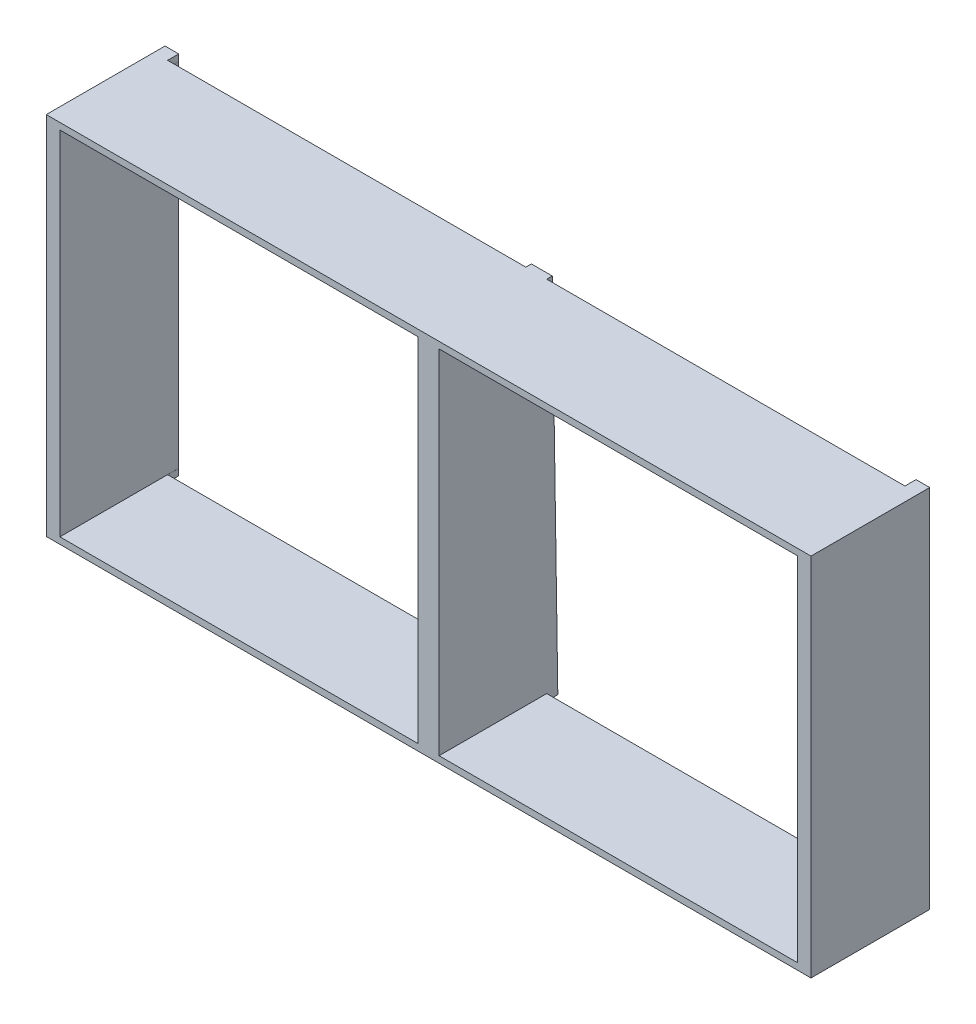
SolidWorks part; units mm, degrees
ref_plane "Спереди" through (0, 0, 0) normal (0, 0, 1) x (1, 0, 0)
ref_plane "Сверху" through (0, 0, 0) normal (0, 1, 0) x (1, 0, 0)
ref_plane "Справа" through (0, 0, 0) normal (1, 0, 0) x (0, 0, -1)
sketch "Эскиз1" plane through (0, 0, 0) normal (0, 0, 1) x (1, 0, 0)
  line L1 (-2930, 1400) -> (2930, 1400)
  line L2 (-2930, 1400) -> (-2930, -1400)
  line L3 (-2930, -1400) -> (2930, -1400)
  line L4 (2930, 1400) -> (2930, -1400)
  line L5 (-2930, 1400) -> (2930, -1400) construction
  line L6 (-2930, -1400) -> (2930, 1400) construction
  line L7 (-2825.3571, 1350) -> (-80, 1350)
  line L8 (-2825.3571, 1350) -> (-2825.3571, -1350)
  line L9 (-2825.3571, -1350) -> (-80, -1350)
  line L10 (-80, 1350) -> (-80, -1350)
  line L11 (80, 1350) -> (2825.3571, 1350)
  line L12 (80, 1350) -> (80, -1350)
  line L13 (80, -1350) -> (2825.3571, -1350)
  line L14 (2825.3571, 1350) -> (2825.3571, -1350)
  point P0 (0, 0)
extrude "Бобышка-Вытянуть1" add sketch "Эскиз1" along normal blind 910
sketch "Эскиз2" plane through (0, -1400, 0) normal (0, -1, 0) x (1, 0, 0)
  line L2 (-2825, 85) -> (-80, 85)
  line L3 (-2825, 85) -> (-2825, 0)
  line L4 (-2825, 0) -> (-80, 0)
  line L5 (-80, 85) -> (-80, 0)
  line L6 (-2825, 85) -> (-80, 0) construction
  line L7 (-2825, 0) -> (-80, 85) construction
  line L8 (0, 424.0898) -> (0, -233.7336) construction
  line L9 (2825, 0) -> (80, 85) construction
  line L10 (2825, 85) -> (80, 0) construction
  line L11 (80, 85) -> (80, 0)
  line L12 (2825, 0) -> (80, 0)
  line L13 (2825, 85) -> (2825, 0)
  line L14 (2825, 85) -> (80, 85)
  line L15 (-2930, 0) -> (2930, 0) construction
  point P2 (-1452.5, 42.5)
  point P15 (1452.5, 42.5)
extrude "Вырез-Вытянуть1" cut sketch "Эскиз2" against normal through all
sketch "Эскиз3" plane through (-80, 0, 0) normal (-1, 0, 0) x (0, 0, 1)
  line L0 (0, 1400) -> (0, -1400)
  line L1 (0, 1400) -> (85, 1400) construction
  line L2 (0, -1400) -> (0, 1400) construction
  line L3 (0, -1400) -> (42.5, 1400)
  line L4 (42.5, 1400) -> (0, 1400)
extrude "Вырез-Вытянуть2" cut sketch "Эскиз3" against normal up to surface (160 mm away) up to face at (80, 0, 270)
